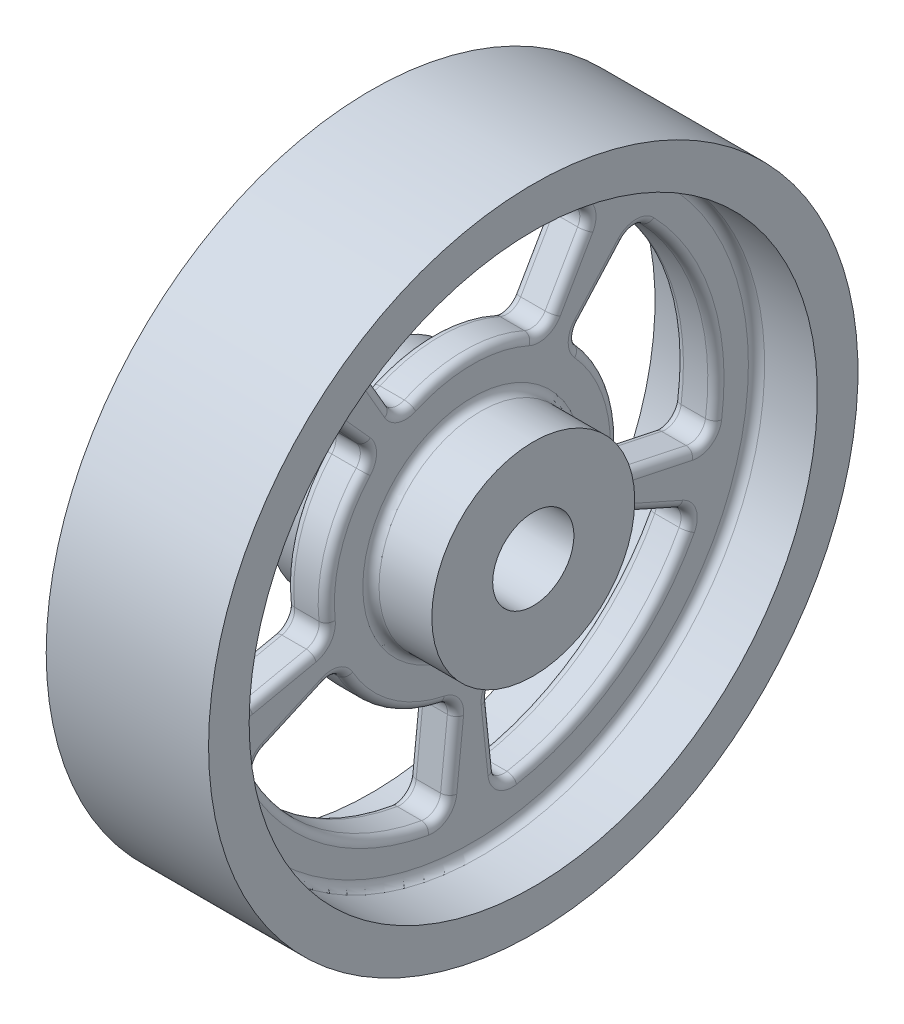
SolidWorks part; units mm, degrees
ref_plane "Front Plane" through (0, 0, 0) normal (0, 0, 1) x (1, 0, 0)
ref_plane "Top Plane" through (0, 0, 0) normal (0, 1, 0) x (1, 0, 0)
ref_plane "Right Plane" through (0, 0, 0) normal (1, 0, 0) x (0, 0, -1)
sketch "Sketch1" plane through (0, 0, 0) normal (0, 0, 1) x (1, 0, 0)
  line L0 (-2.5, 35) -> (-10, 35)
  line L1 (10, 5) -> (-10, 5)
  line L2 (10, 5) -> (10, 12.5)
  line L3 (10, 12.5) -> (2.5, 12.5)
  line L4 (-10, 5) -> (-10, 12.5)
  line L5 (0, 0) -> (45.6338, 0) construction
  line L6 (-2.5, 12.5) -> (-2.5, 35)
  line L7 (0, 0) -> (0, 47.8253) construction
  line L8 (2.5, 12.5) -> (2.5, 35)
  line L9 (10, 35) -> (2.5, 35)
  line L10 (10, 35) -> (10, 40)
  line L11 (10, 40) -> (-10, 40)
  line L12 (-10, 35) -> (-10, 40)
  line L13 (-2.5, 12.5) -> (-10, 12.5)
  point P21 (0, 5)
  dimension "D1" = 20
  dimension "D2" = 5
  dimension "D3" = 5
  dimension "D4" = 5
  dimension "D5" = 12.5
  dimension "D6" = 40
revolve "Revolve1" add sketch "Sketch1" angle 360 mid plane about L5
sketch "Sketch2" plane through (2.5, 0, 0) normal (1, 0, 0) x (0, 0, -1)
  line L0 (0, 0) -> (0, 43.3836) construction
  line L1 (-15, 25.9808) -> (-9, 15.5885)
  line L2 (15, 25.9808) -> (9, 15.5885)
  arc A0 (15, 25.9808) -> (-15, 25.9808) centre (0, 0) ccw
  arc A1 (9, 15.5885) -> (-9, 15.5885) centre (0, 0) ccw
  point P6 (0, 30)
  point P8 (0, 18)
  dimension "D1" = 18
  dimension "D2" = 30
  dimension "D3" = 60
extrude "Cut-Extrude1" cut sketch "Sketch2" against normal blind 10
fillet "Fillet1" radius 2 4 edges at (0, 25.9808, 15) (0, 25.9808, -15) (0, 15.5885, 9) (0, 15.5885, -9)
pattern_circular "CirPattern1" count 5 over 360 about axis through (0, 0, 0) along (1, 0, 0) of "Fillet1", "Cut-Extrude1"
fillet "Fillet2" radius 1 84 edges at (-2.5, -5.4877, -28.8825) (-2.5, -4.972, -23.3915) (-2.5, -3.353, -18.26) (-2.5, 5.5623, -17.119) (-2.5, 13.4456, -12.8018) (-2.5, 17.7717, -16.0017) (-2.5, 21.4164, -20.1409) (2.5, -5.4877, -28.8825) (2.5, -4.972, -23.3915) (2.5, -3.353, -18.26) (2.5, 5.5623, -17.119) (2.5, 13.4456, -12.8018) (2.5, 17.7717, -16.0017) (2.5, 21.4164, -20.1409) (-2.5, -12.5371, 26.592) (-2.5, -9.7267, 21.8466) (-2.5, -8.0203, 16.7435) (-2.5, -14.5623, 10.5801) (-2.5, -18.4024, 2.4538) (-2.5, -23.7831, 2.4997) (-2.5, -29.1647, 3.7061) (2.5, -12.5371, 26.592) (2.5, -9.7267, 21.8466) (2.5, -8.0203, 16.7435) (2.5, -14.5623, 10.5801) (2.5, -18.4024, 2.4538) (2.5, -23.7831, 2.4997) (2.5, -29.1647, 3.7061) (-2.5, 25.7731, -14.1443) (-2.5, 20.7102, -11.9571) (-2.5, 16.3302, -8.8315) (-2.5, 18, 0) (-2.5, 16.3302, 8.8315) (-2.5, 20.7102, 11.9571) (-2.5, 25.7731, 14.1443) (2.5, 25.7731, -14.1443) (2.5, 20.7102, -11.9571) (2.5, 16.3302, -8.8315) (2.5, 18, 0) (2.5, 16.3302, 8.8315) (2.5, 20.7102, 11.9571) (2.5, 25.7731, 14.1443) (-2.5, 21.4164, 20.1409) (-2.5, 17.7717, 16.0017) (-2.5, 13.4456, 12.8018) (-2.5, 5.5623, 17.119) (-2.5, -3.353, 18.26) (-2.5, -4.972, 23.3915) (-2.5, -5.4877, 28.8825) (2.5, 21.4164, 20.1409) (2.5, 17.7717, 16.0017) (2.5, 13.4456, 12.8018) (2.5, 5.5623, 17.119) (2.5, -3.353, 18.26) (2.5, -4.972, 23.3915) (2.5, -5.4877, 28.8825) (-2.5, -29.1647, -3.7061) (-2.5, -23.7831, -2.4997) (-2.5, -18.4024, -2.4538) (-2.5, -14.5623, -10.5801) (-2.5, -8.0203, -16.7435) (-2.5, -9.7267, -21.8466) (-2.5, -12.5371, -26.592) (2.5, -29.1647, -3.7061) (2.5, -23.7831, -2.4997) (2.5, -18.4024, -2.4538) (2.5, -14.5623, -10.5801) (2.5, -8.0203, -16.7435) (2.5, -9.7267, -21.8466) (2.5, -12.5371, -26.592) (-2.5, 9.2705, -28.5317) (2.5, 9.2705, -28.5317) (-2.5, -24.2705, 17.6336) (2.5, -24.2705, 17.6336) (-2.5, 30, 0) (2.5, 30, 0) (-2.5, 9.2705, 28.5317) (2.5, 9.2705, 28.5317) (-2.5, -24.2705, -17.6336) (2.5, -24.2705, -17.6336) (2.5, 0, 12.5) (-2.5, 0, 12.5) (-2.5, 0, 35) (2.5, 0, 35)
